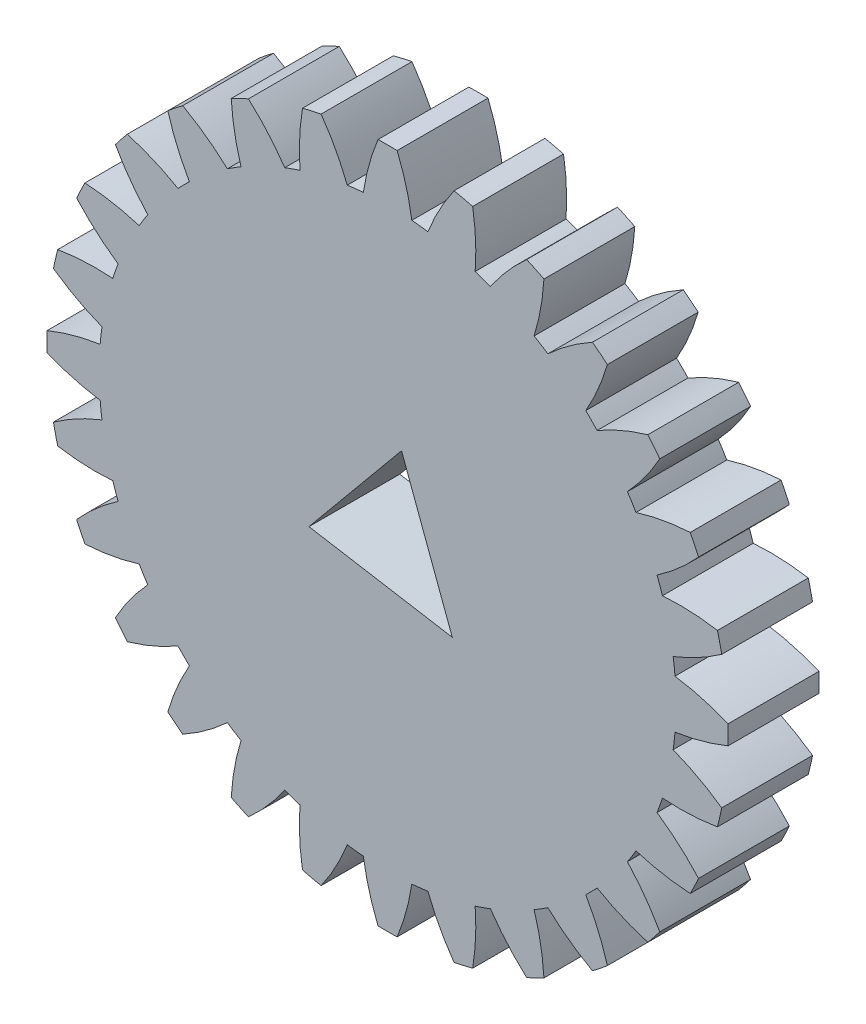
SolidWorks part; units mm, degrees
ref_plane "Front Plane" through (0, 0, 0) normal (0, 0, 1) x (1, 0, 0)
ref_plane "Top Plane" through (0, 0, 0) normal (0, 1, 0) x (1, 0, 0)
ref_plane "Right Plane" through (0, 0, 0) normal (1, 0, 0) x (0, 0, -1)
ref_plane "Plane1" through (0, 0, 5) normal (0, 0, 1) x (1, 0, 0)
sketch "Sketch1" plane through (0, 0, 5) normal (0, 0, 1) x (1, 0, 0)
  line L0 (0.768, 4.5545) -> (3.5603, -2.9424)
  line L1 (3.5603, -2.9424) -> (-4.3283, -1.6121)
  line L2 (-4.3283, -1.6121) -> (0.768, 4.5545)
  line L3 (0, 0) -> (-1.7774, 15.7752) construction
  line L4 (0, 0) -> (4.681, 27.7597) construction
  line L5 (0, 0) -> (3.5603, -2.9424) construction
  line L6 (0, 0) -> (-4.3283, -1.6121) construction
  arc A0 (-4.8209, 15.1253) -> (-5.6614, 14.8312) centre (0, 0) ccw
  arc A1 (-5.6614, 14.8312) -> (-7.6583, 17.1147) centre (-16.0015, 7.8034) ccw
  arc A2 (-7.6583, 17.1147) -> (-8.6059, 16.6584) centre (0, 0) ccw
  arc A3 (-8.6059, 16.6584) -> (-8.0657, 13.6733) centre (3.8758, 17.3758) ccw
  arc A4 (-8.0657, 13.6733) -> (-8.8197, 13.1996) centre (0, 0) ccw
  arc A5 (-8.8197, 13.1996) -> (-11.2747, 14.9814) centre (-17.3368, 4.0471) ccw
  arc A6 (-11.2747, 14.9814) -> (-12.097, 14.3257) centre (0, 0) ccw
  arc A7 (-12.097, 14.3257) -> (-10.9061, 11.5357) centre (-0.0878, 17.8027) ccw
  arc A8 (-10.9061, 11.5357) -> (-11.5357, 10.9061) centre (0, 0) ccw
  arc A9 (-11.5357, 10.9061) -> (-14.3257, 12.097) centre (-17.8027, 0.0878) ccw
  arc A10 (-14.3257, 12.097) -> (-14.9814, 11.2747) centre (0, 0) ccw
  arc A11 (-14.9814, 11.2747) -> (-13.1996, 8.8197) centre (-4.0471, 17.3368) ccw
  arc A12 (-13.1996, 8.8197) -> (-13.6733, 8.0657) centre (0, 0) ccw
  arc A13 (-13.6733, 8.0657) -> (-16.6584, 8.6059) centre (-17.3758, -3.8758) ccw
  arc A14 (-16.6584, 8.6059) -> (-17.1147, 7.6583) centre (0, 0) ccw
  arc A15 (-17.1147, 7.6583) -> (-14.8312, 5.6614) centre (-7.8034, 16.0015) ccw
  arc A16 (-14.8312, 5.6614) -> (-15.1253, 4.8209) centre (0, 0) ccw
  arc A17 (-15.1253, 4.8209) -> (-18.1557, 4.6833) centre (-16.0777, -7.6452) ccw
  arc A18 (-18.1557, 4.6833) -> (-18.3897, 3.6579) centre (0, 0) ccw
  arc A19 (-18.3897, 3.6579) -> (-15.7191, 2.2192) centre (-11.1684, 13.8639) ccw
  arc A20 (-15.7191, 2.2192) -> (-15.8188, 1.3343) centre (0, 0) ccw
  arc A21 (-15.8188, 1.3343) -> (-18.7426, 0.5259) centre (-13.9734, -11.0311) ccw
  arc A22 (-18.7426, 0.5259) -> (-18.7426, -0.5259) centre (0, 0) ccw
  arc A23 (-18.7426, -0.5259) -> (-15.8188, -1.3343) centre (-13.9734, 11.0311) ccw
  arc A24 (-15.8188, -1.3343) -> (-15.7191, -2.2192) centre (0, 0) ccw
  arc A25 (-15.7191, -2.2192) -> (-18.3897, -3.6579) centre (-11.1684, -13.8639) ccw
  arc A26 (-18.3897, -3.6579) -> (-18.1557, -4.6833) centre (0, 0) ccw
  arc A27 (-18.1557, -4.6833) -> (-15.1253, -4.8209) centre (-16.0777, 7.6452) ccw
  arc A28 (-15.1253, -4.8209) -> (-14.8312, -5.6614) centre (0, 0) ccw
  arc A29 (-14.8312, -5.6614) -> (-17.1147, -7.6583) centre (-7.8034, -16.0015) ccw
  arc A30 (-17.1147, -7.6583) -> (-16.6584, -8.6059) centre (0, 0) ccw
  arc A31 (-16.6584, -8.6059) -> (-13.6733, -8.0657) centre (-17.3758, 3.8758) ccw
  arc A32 (-13.6733, -8.0657) -> (-13.1996, -8.8197) centre (0, 0) ccw
  arc A33 (-13.1996, -8.8197) -> (-14.9814, -11.2747) centre (-4.0471, -17.3368) ccw
  arc A34 (-14.9814, -11.2747) -> (-14.3257, -12.097) centre (0, 0) ccw
  arc A35 (-14.3257, -12.097) -> (-11.5357, -10.9061) centre (-17.8027, -0.0878) ccw
  arc A36 (-11.5357, -10.9061) -> (-10.9061, -11.5357) centre (0, 0) ccw
  arc A37 (-10.9061, -11.5357) -> (-12.097, -14.3257) centre (-0.0878, -17.8027) ccw
  arc A38 (-12.097, -14.3257) -> (-11.2747, -14.9814) centre (0, 0) ccw
  arc A39 (-11.2747, -14.9814) -> (-8.8197, -13.1996) centre (-17.3368, -4.0471) ccw
  arc A40 (-8.8197, -13.1996) -> (-8.0657, -13.6733) centre (0, 0) ccw
  arc A41 (-8.0657, -13.6733) -> (-8.6059, -16.6584) centre (3.8758, -17.3758) ccw
  arc A42 (-8.6059, -16.6584) -> (-7.6583, -17.1147) centre (0, 0) ccw
  arc A43 (-7.6583, -17.1147) -> (-5.6614, -14.8312) centre (-16.0015, -7.8034) ccw
  arc A44 (-5.6614, -14.8312) -> (-4.8209, -15.1253) centre (0, 0) ccw
  arc A45 (-4.8209, -15.1253) -> (-4.6833, -18.1557) centre (7.6452, -16.0777) ccw
  arc A46 (-4.6833, -18.1557) -> (-3.6579, -18.3897) centre (0, 0) ccw
  arc A47 (-3.6579, -18.3897) -> (-2.2192, -15.7191) centre (-13.8639, -11.1684) ccw
  arc A48 (-2.2192, -15.7191) -> (-1.3343, -15.8188) centre (0, 0) ccw
  arc A49 (-1.3343, -15.8188) -> (-0.5259, -18.7426) centre (11.0311, -13.9734) ccw
  arc A50 (-0.5259, -18.7426) -> (0.5259, -18.7426) centre (0, 0) ccw
  arc A51 (0.5259, -18.7426) -> (1.3343, -15.8188) centre (-11.0311, -13.9734) ccw
  arc A52 (1.3343, -15.8188) -> (2.2192, -15.7191) centre (0, 0) ccw
  arc A53 (2.2192, -15.7191) -> (3.6579, -18.3897) centre (13.8639, -11.1684) ccw
  arc A54 (3.6579, -18.3897) -> (4.6833, -18.1557) centre (0, 0) ccw
  arc A55 (4.6833, -18.1557) -> (4.8209, -15.1253) centre (-7.6452, -16.0777) ccw
  arc A56 (4.8209, -15.1253) -> (5.6614, -14.8312) centre (0, 0) ccw
  arc A57 (5.6614, -14.8312) -> (7.6583, -17.1147) centre (16.0015, -7.8034) ccw
  arc A58 (7.6583, -17.1147) -> (8.6059, -16.6584) centre (0, 0) ccw
  arc A59 (8.6059, -16.6584) -> (8.0657, -13.6733) centre (-3.8758, -17.3758) ccw
  arc A60 (8.0657, -13.6733) -> (8.8197, -13.1996) centre (0, 0) ccw
  arc A61 (8.8197, -13.1996) -> (11.2747, -14.9814) centre (17.3368, -4.0471) ccw
  arc A62 (11.2747, -14.9814) -> (12.097, -14.3257) centre (0, 0) ccw
  arc A63 (12.097, -14.3257) -> (10.9061, -11.5357) centre (0.0878, -17.8027) ccw
  arc A64 (10.9061, -11.5357) -> (11.5357, -10.9061) centre (0, 0) ccw
  arc A65 (11.5357, -10.9061) -> (14.3257, -12.097) centre (17.8027, -0.0878) ccw
  arc A66 (14.3257, -12.097) -> (14.9814, -11.2747) centre (0, 0) ccw
  arc A67 (14.9814, -11.2747) -> (13.1996, -8.8197) centre (4.0471, -17.3368) ccw
  arc A68 (13.1996, -8.8197) -> (13.6733, -8.0657) centre (0, 0) ccw
  arc A69 (13.6733, -8.0657) -> (16.6584, -8.6059) centre (17.3758, 3.8758) ccw
  arc A70 (16.6584, -8.6059) -> (17.1147, -7.6583) centre (0, 0) ccw
  arc A71 (17.1147, -7.6583) -> (14.8312, -5.6614) centre (7.8034, -16.0015) ccw
  arc A72 (14.8312, -5.6614) -> (15.1253, -4.8209) centre (0, 0) ccw
  arc A73 (15.1253, -4.8209) -> (18.1557, -4.6833) centre (16.0777, 7.6452) ccw
  arc A74 (18.1557, -4.6833) -> (18.3897, -3.6579) centre (0, 0) ccw
  arc A75 (18.3897, -3.6579) -> (15.7191, -2.2192) centre (11.1684, -13.8639) ccw
  arc A76 (15.7191, -2.2192) -> (15.8188, -1.3343) centre (0, 0) ccw
  arc A77 (15.8188, -1.3343) -> (18.7426, -0.5259) centre (13.9734, 11.0311) ccw
  arc A78 (18.7426, -0.5259) -> (18.7426, 0.5259) centre (0, 0) ccw
  arc A79 (18.7426, 0.5259) -> (15.8188, 1.3343) centre (13.9734, -11.0311) ccw
  arc A80 (15.8188, 1.3343) -> (15.7191, 2.2192) centre (0, 0) ccw
  arc A81 (15.7191, 2.2192) -> (18.3897, 3.6579) centre (11.1684, 13.8639) ccw
  arc A82 (18.3897, 3.6579) -> (18.1557, 4.6833) centre (0, 0) ccw
  arc A83 (18.1557, 4.6833) -> (15.1253, 4.8209) centre (16.0777, -7.6452) ccw
  arc A84 (15.1253, 4.8209) -> (14.8312, 5.6614) centre (0, 0) ccw
  arc A85 (14.8312, 5.6614) -> (17.1147, 7.6583) centre (7.8034, 16.0015) ccw
  arc A86 (17.1147, 7.6583) -> (16.6584, 8.6059) centre (0, 0) ccw
  arc A87 (16.6584, 8.6059) -> (13.6733, 8.0657) centre (17.3758, -3.8758) ccw
  arc A88 (13.6733, 8.0657) -> (13.1996, 8.8197) centre (0, 0) ccw
  arc A89 (13.1996, 8.8197) -> (14.9814, 11.2747) centre (4.0471, 17.3368) ccw
  arc A90 (14.9814, 11.2747) -> (14.3257, 12.097) centre (0, 0) ccw
  arc A91 (14.3257, 12.097) -> (11.5357, 10.9061) centre (17.8027, 0.0878) ccw
  arc A92 (11.5357, 10.9061) -> (10.9061, 11.5357) centre (0, 0) ccw
  arc A93 (10.9061, 11.5357) -> (12.097, 14.3257) centre (0.0878, 17.8027) ccw
  arc A94 (12.097, 14.3257) -> (11.2747, 14.9814) centre (0, 0) ccw
  arc A95 (11.2747, 14.9814) -> (8.8197, 13.1996) centre (17.3368, 4.0471) ccw
  arc A96 (8.8197, 13.1996) -> (8.0657, 13.6733) centre (0, 0) ccw
  arc A97 (8.0657, 13.6733) -> (8.6059, 16.6584) centre (-3.8758, 17.3758) ccw
  arc A98 (8.6059, 16.6584) -> (7.6583, 17.1147) centre (0, 0) ccw
  arc A99 (7.6583, 17.1147) -> (5.6614, 14.8312) centre (16.0015, 7.8034) ccw
  arc A100 (5.6614, 14.8312) -> (4.8209, 15.1253) centre (0, 0) ccw
  arc A101 (4.8209, 15.1253) -> (4.6833, 18.1557) centre (-7.6452, 16.0777) ccw
  arc A102 (4.6833, 18.1557) -> (3.6579, 18.3897) centre (0, 0) ccw
  arc A103 (3.6579, 18.3897) -> (2.2192, 15.7191) centre (13.8639, 11.1684) ccw
  arc A104 (2.2192, 15.7191) -> (1.3343, 15.8188) centre (0, 0) ccw
  arc A105 (1.3343, 15.8188) -> (0.5259, 18.7426) centre (-11.0311, 13.9734) ccw
  arc A106 (0.5259, 18.7426) -> (-0.5259, 18.7426) centre (0, 0) ccw
  arc A107 (-0.5259, 18.7426) -> (-1.3343, 15.8188) centre (11.0311, 13.9734) ccw
  arc A108 (-1.3343, 15.8188) -> (-2.2192, 15.7191) centre (0, 0) ccw
  arc A109 (-2.2192, 15.7191) -> (-3.6579, 18.3897) centre (-13.8639, 11.1684) ccw
  arc A110 (-3.6579, 18.3897) -> (-4.6833, 18.1557) centre (0, 0) ccw
  arc A111 (-4.6833, 18.1557) -> (-4.8209, 15.1253) centre (7.6452, 16.0777) ccw
  dimension "D1" = 16
  dimension "D2" = 8
  dimension "D3" = 8
  dimension "D4" = 8
  dimension "D5" = 4.6188
extrude "Boss-Extrude1" add sketch "Sketch1" against normal blind 5
